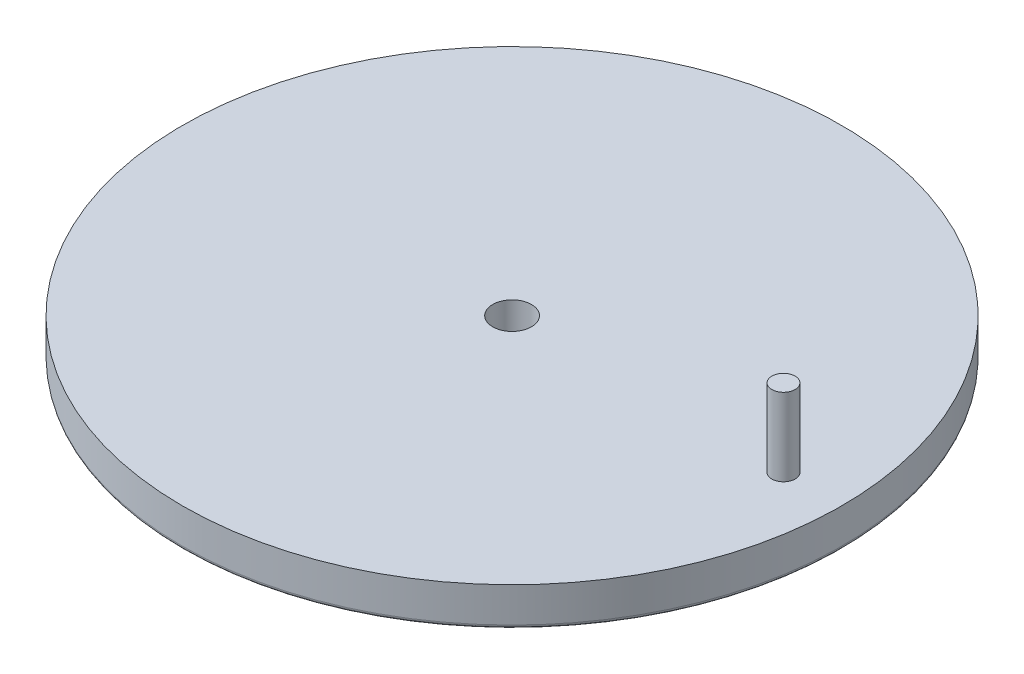
SolidWorks part; units mm, degrees
ref_plane "Front Plane" through (0, 0, 0) normal (0, 0, 1) x (1, 0, 0)
ref_plane "Top Plane" through (0, 0, 0) normal (0, 1, 0) x (1, 0, 0)
ref_plane "Right Plane" through (0, 0, 0) normal (1, 0, 0) x (0, 0, -1)
sketch "Sketch1" plane through (0, 0, 0) normal (0, 1, 0) x (1, 0, 0)
  circle A0 centre (0, 0) radius 42.5
  dimension "D1" = 85
extrude "Boss-Extrude1" add sketch "Sketch1" along normal blind 5
sketch "Sketch2" plane through (0, 5, 0) normal (0, 1, 0) x (1, 0, 0)
  line L0 (0, 0) -> (0, -42.5) construction
  line L1 (0, 0) -> (42.5, 0) construction
  circle A0 centre (0, 0) radius 42.5 construction
  circle A1 centre (35, 0) radius 1.5
  dimension "D1" = 3
  dimension "D2" = 35
extrude "Boss-Extrude2" add sketch "Sketch2" along normal blind 10
sketch "Sketch3" plane through (0, 5, 0) normal (0, 1, 0) x (1, 0, 0)
  circle A0 centre (0, 0) radius 2.5
  dimension "D1" = 5
extrude "Cut-Extrude1" cut sketch "Sketch3" against normal blind 10
sketch "Sketch4" plane through (0, 0, 0) normal (0, -1, 0) x (1, 0, 0)
  line L0 (0, 0) -> (0, -42.5) construction
  circle A0 centre (0, 0) radius 42.5 construction
  circle A1 centre (0, -35) radius 5
  dimension "D1" = 10
  dimension "D2" = 35
extrude "Boss-Extrude3" add sketch "Sketch4" along normal blind 10
fillet "Fillet1" radius 0.5 1 edges at (0, 0, 42.5)
